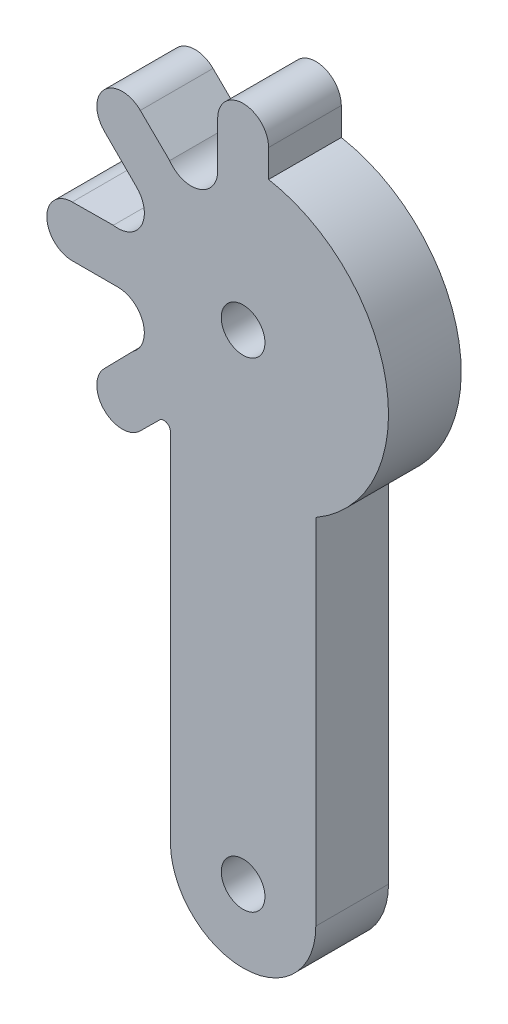
SolidWorks part; units mm, degrees
material "Acrylic (Medium-high impact)"
ref_plane "Front Plane" through (0, 0, 0) normal (0, 0, 1) x (1, 0, 0)
ref_plane "Top Plane" through (0, 0, 0) normal (0, 1, 0) x (1, 0, 0)
ref_plane "Right Plane" through (0, 0, 0) normal (1, 0, 0) x (0, 0, -1)
sketch "Sketch2" plane through (0, 0, 0) normal (0, 0, 1) x (1, 0, 0)
  line L0 (0, 0) -> (0, -33) construction
  line L1 (5, -8.6603) -> (5, -33)
  line L2 (-5, -8.5428) -> (-5, -33)
  line L3 (0, 0) -> (0, 27.439) construction
  line L6 (-1.7473, 11.75) -> (-1.7473, 8.6066)
  line L8 (1.7527, 11.7496) -> (1.7527, 9.8452)
  line L17 (-9.5476, -7.0689) -> (-7.5701, -5.0511)
  line L18 (-7.073, -9.544) -> (-5.7503, -8.2305)
  line L19 (-11.7496, 1.7527) -> (-8.9245, 1.7812)
  line L20 (-11.75, -1.7473) -> (-8.6066, -1.7473)
  line L21 (-7.0689, 9.5476) -> (-5.0511, 7.5701)
  line L22 (-9.544, 7.073) -> (-7.3213, 4.8503)
  arc A1 (-5, -33) -> (5, -33) centre (0, -33) ccw
  circle A3 centre (0, -33) radius 1.5
  circle A4 centre (0, 0) radius 13.5 construction
  circle A5 centre (0, 0) radius 7.5 construction
  arc A15 (1.7527, 11.7496) -> (-1.7473, 11.75) centre (0.0027, 11.75) ccw
  circle A24 centre (0, 0) radius 1.5
  arc A25 (5, -8.6603) -> (1.7527, 9.8452) centre (0, 0) ccw
  arc A27 (-5.0511, 7.5701) -> (-1.7473, 8.6066) centre (-3.5618, 8.6066) ccw
  arc A28 (-5, -8.5428) -> (-5.7503, -8.2305) centre (-5.4401, -8.5428) ccw
  arc A30 (-9.5476, -7.0689) -> (-7.073, -9.544) centre (-8.3104, -8.3066) ccw
  arc A31 (-11.7496, 1.7527) -> (-11.75, -1.7473) centre (-11.7498, 0.0027) ccw
  arc A32 (-7.0689, 9.5476) -> (-9.544, 7.073) centre (-8.3064, 8.3103) ccw
  arc A36 (-7.5701, -5.0511) -> (-8.6066, -1.7473) centre (-8.6066, -3.5618) ccw
  arc A37 (-8.9245, 1.7812) -> (-7.3213, 4.8503) centre (-8.6044, 3.5672) ccw
  arc A38 (1.7812, 8.9245) -> (4.8503, 7.3213) centre (3.5672, 8.6044) ccw [skipped]
  arc A39 (7.5701, 5.0511) -> (8.6066, 1.7473) centre (8.6066, 3.5618) ccw [skipped]
  arc A40 (8.9245, -1.7812) -> (7.3213, -4.8503) centre (8.6044, -3.5672) ccw [skipped]
  arc A41 (5.0511, -7.5701) -> (1.7473, -8.6066) centre (3.5618, -8.6066) ccw [skipped]
  arc A42 (-1.7812, -8.9245) -> (-4.8503, -7.3213) centre (-3.5672, -8.6044) ccw [skipped]
  point P3 (0, -16.5)
  dimension "D1" = 5
  dimension "D2" = 8
  dimension "D8" = 3
  dimension "D9" = 27
  dimension "D10" = 15
  dimension "D11" = 3.5
  dimension "D3" = 24.3397
  dimension "D4" = 33
  dimension "D5" = 5
  dimension "D6" = 5
extrude "Boss-Extrude1" add sketch "Sketch2" along normal blind 5
